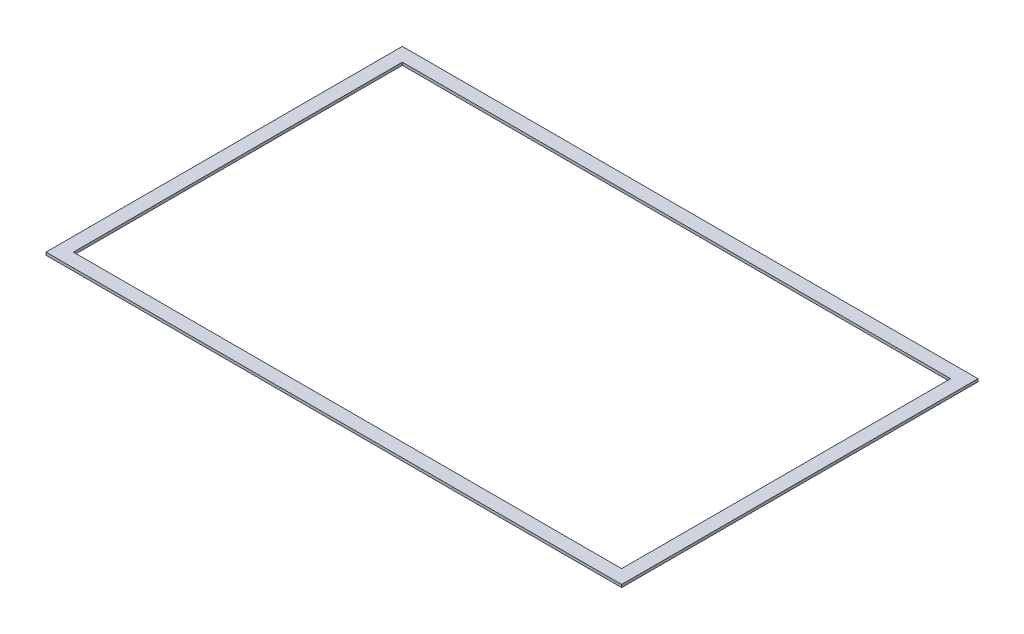
SolidWorks part; units mm, degrees
ref_plane "Front Plane" through (0, 0, 0) normal (0, 0, 1) x (1, 0, 0)
ref_plane "Top Plane" through (0, 0, 0) normal (0, 1, 0) x (1, 0, 0)
ref_plane "Right Plane" through (0, 0, 0) normal (1, 0, 0) x (0, 0, -1)
sketch "Sketch1" plane through (0, 0, 0) normal (0, 1, 0) x (1, 0, 0)
  line L1 (-100, -60) -> (100, -60)
  line L2 (-100, -60) -> (-100, 60)
  line L3 (-100, 60) -> (100, 60)
  line L4 (100, -60) -> (100, 60)
  line L5 (-100, -60) -> (100, 60) construction
  line L6 (-100, 60) -> (100, -60) construction
  line L7 (-105, -65) -> (105, -65)
  line L8 (-105, -65) -> (-105, 65)
  line L9 (-105, 65) -> (105, 65)
  line L10 (105, -65) -> (105, 65)
  line L11 (-105, -65) -> (105, 65) construction
  line L12 (-105, 65) -> (105, -65) construction
  point P0 (0, 0)
  point P6 (0, 0)
  dimension "D1" = 200
  dimension "D2" = 120
  dimension "D3" = 210
  dimension "D4" = 130
extrude "Boss-Extrude1" add sketch "Sketch1" along normal blind 1
